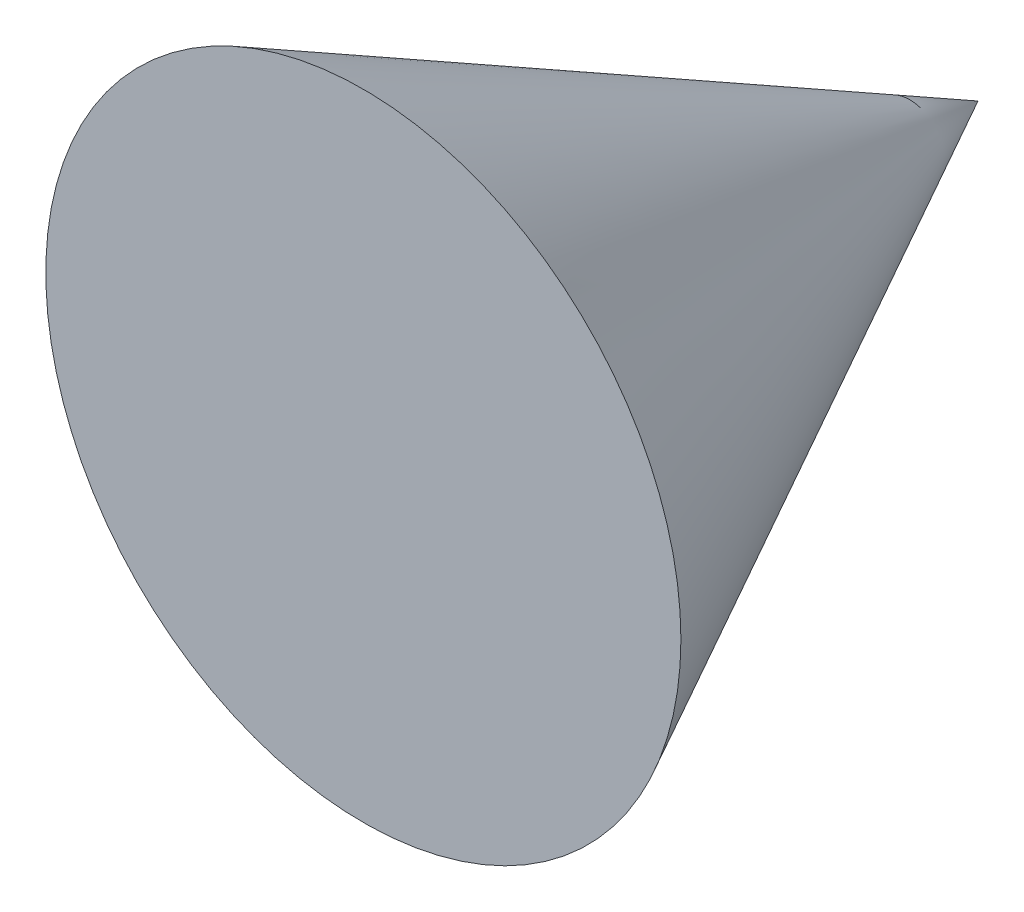
SolidWorks part; units mm, degrees
ref_plane "Front Plane" through (0, 0, 0) normal (0, 0, 1) x (1, 0, 0)
ref_plane "Top Plane" through (0, 0, 0) normal (0, 1, 0) x (1, 0, 0)
ref_plane "Right Plane" through (0, 0, 0) normal (1, 0, 0) x (0, 0, -1)
sketch "Sketch1" plane through (0, 0, 0) normal (0, 1, 0) x (1, 0, 0)
  line L0 (0, 0) -> (0, 300)
  line L1 (0, 300) -> (155, 0)
  line L2 (155, 0) -> (0, 0)
  dimension "D1" = 300
  dimension "D2" = 155
revolve "Revolve1" add sketch "Sketch1" angle 360 about L0
